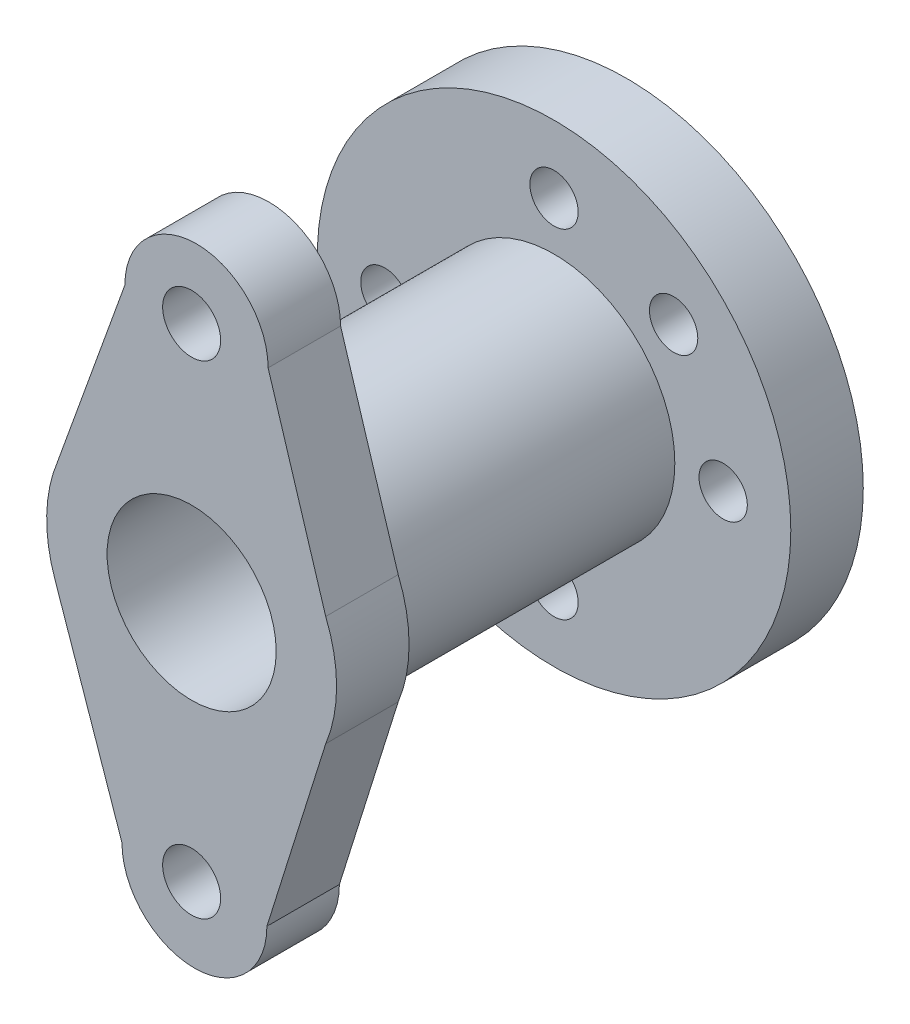
SolidWorks part; units mm, degrees
ref_plane "Front Plane" through (0, 0, 0) normal (0, 0, 1) x (1, 0, 0)
ref_plane "Top Plane" through (0, 0, 0) normal (0, 1, 0) x (1, 0, 0)
ref_plane "Right Plane" through (0, 0, 0) normal (1, 0, 0) x (0, 0, -1)
sketch "Sketch1" plane through (0, 0, 0) normal (0, 0, 1) x (1, 0, 0)
  circle A0 centre (2.001, -3.5017) radius 49
  circle A1 centre (2.001, -3.5017) radius 35 construction
  circle A3 centre (2.001, 31.4983) radius 5
  circle A4 centre (37.001, -3.5017) radius 5
  circle A5 centre (2.001, -38.5017) radius 5
  circle A6 centre (-32.999, -3.5017) radius 5
  circle A7 centre (26.7497, 21.2471) radius 5
  circle A8 centre (-22.7478, -28.2504) radius 5
extrude "Boss-Extrude1" add sketch "Sketch1" along normal blind 15
sketch "Sketch2" plane through (0, 0, 15) normal (0, 0, 1) x (1, 0, 0)
  circle A0 centre (2.001, -3.5017) radius 25
extrude "Boss-Extrude2" add sketch "Sketch2" along normal blind 60
sketch3d "3DSketch1"
  line L0 (17.8286, 46.4983, 90) -> (29.7478, 7.9051, 90)
  line L1 (-11.8199, 46.4983, 90) -> (-25.7459, 7.9051, 90)
  line L2 (17.5793, -53.7079, 90) -> (29.7478, -14.9085, 90)
  line L3 (-12.4207, -53.7079, 90) -> (-26.2568, -13.5763, 90)
  line L4 (2.001, -3.5017, 90) -> (2.001, 40.2921, 90) construction
  line L5 (2.001, -3.5017, 90) -> (2.001, -53.5029, 90) construction
  line L6 (2.001, -3.5017, 90) -> (2.001, 46.5011, 90) construction
  circle A2 centre (2.001, -3.5017, 90) radius 17.5
  arc A3 (17.8286, 46.4983, 90) -> (-11.8199, 46.4983, 90) centre (3.0044, 46.4983, 90) ccw
  arc A4 (-12.4207, -53.7079, 90) -> (17.5793, -53.7079, 90) centre (2.5793, -53.7079, 90) ccw
  arc A5 (29.7478, -14.9085, 90) -> (29.7478, 7.9051, 90) centre (2.001, -3.5017, 90) ccw
  arc A6 (-25.7459, 7.9051, 90) -> (-26.2568, -13.5763, 90) centre (2.001, -3.5017, 90) ccw
  circle A11 centre (2.001, -53.5029, 90) radius 6
  circle A12 centre (2.001, 46.5011, 90) radius 6
  point P2 (2.001, -3.5017, 107.5)
  point P3 (2.001, -3.5017, 120)
  point P4 (2.001, -3.5017, 120)
  point P7 (3.0044, 46.4983, 104.8242)
  point P11 (2.5793, -53.7079, 105)
  point P20 (2.001, -53.5029, 96)
  point P23 (2.001, 46.5011, 96)
extrude "Boss-Extrude3" add sketch "3DSketch1" along direction (0, 0, 1) on the side of the normal blind 15
sketch "Sketch3" plane through (0, 0, 75) normal (0, 0, 1) x (1, 0, 0)
  circle A0 centre (2.001, -3.5017) radius 17.5
extrude "Cut-Extrude1" cut sketch "Sketch3" against normal blind 60
